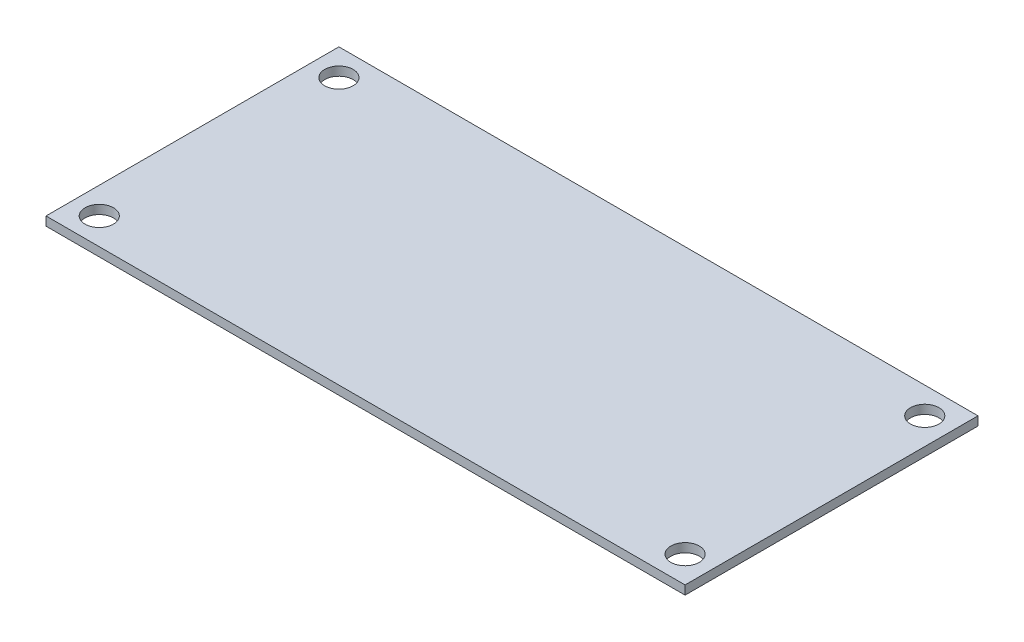
SolidWorks part; units mm, degrees
ref_plane "正面(Front)" through (0, 0, 0) normal (0, 0, 1) x (1, 0, 0)
ref_plane "平面(Top)" through (0, 0, 0) normal (0, 1, 0) x (1, 0, 0)
ref_plane "右側面(Right)" through (0, 0, 0) normal (1, 0, 0) x (0, 0, -1)
sketch "ｽｹｯﾁ2" plane through (0, 0, 0) normal (0, 1, 0) x (1, 0, 0)
  line L1 (-36, 16.5) -> (36, 16.5)
  line L2 (-36, 16.5) -> (-36, -16.5)
  line L3 (-36, -16.5) -> (36, -16.5)
  line L4 (36, 16.5) -> (36, -16.5)
  line L5 (-36, 16.5) -> (36, -16.5) construction
  line L6 (-36, -16.5) -> (36, 16.5) construction
  point P0 (0, 0)
  dimension "D1" = 33
  dimension "D2" = 72
extrude "ﾎﾞｽ - 押し出し1" add sketch "ｽｹｯﾁ2" along normal blind 1
sketch "ｽｹｯﾁ3" plane through (0, 1, 0) normal (0, 1, 0) x (1, 0, 0)
  line L0 (36, -16.5) -> (36, 16.5) construction
  line L1 (36, 16.5) -> (-36, 16.5) construction
  line L2 (0, 0) -> (0, 25.0292) construction
  line L3 (0, 0) -> (41.2743, 0) construction
  circle A0 centre (33, 13.5) radius 1.6
  circle A1 centre (33, -13.5) radius 1.6
  circle A2 centre (-33, -13.5) radius 1.6
  circle A3 centre (-33, 13.5) radius 1.6
  dimension "D1" = 3
  dimension "D2" = 3
  dimension "D3" = 3.2
extrude "ｶｯﾄ - 押し出し1" cut sketch "ｽｹｯﾁ3" against normal through all
